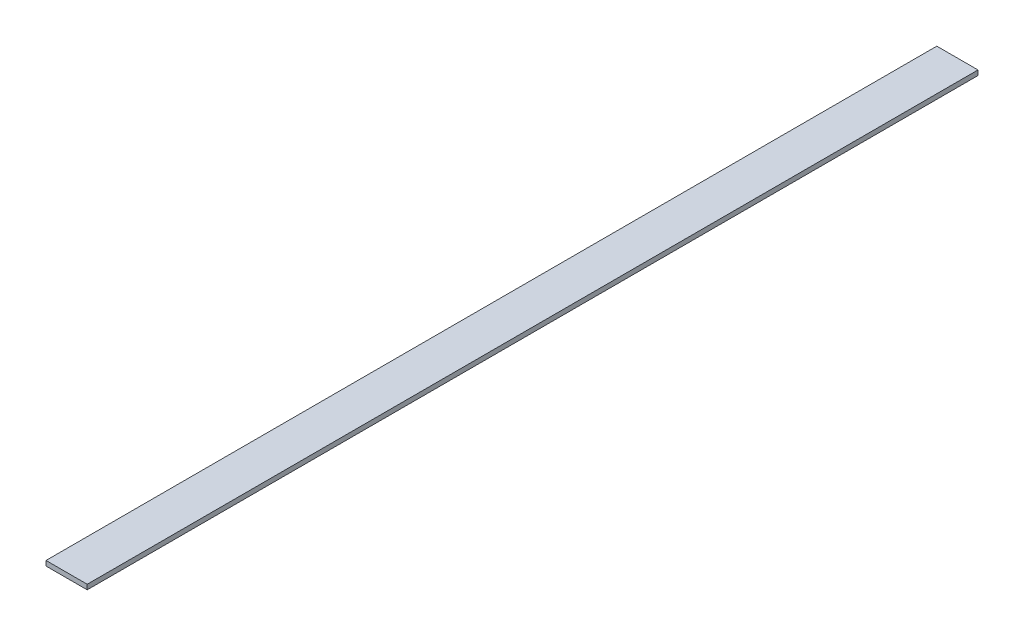
SolidWorks part; units mm, degrees
material "6063-T1"
ref_plane "Front Plane" through (0, 0, 0) normal (0, 0, 1) x (1, 0, 0)
ref_plane "Top Plane" through (0, 0, 0) normal (0, 1, 0) x (1, 0, 0)
ref_plane "Right Plane" through (0, 0, 0) normal (1, 0, 0) x (0, 0, -1)
sketch "Sketch1" plane through (0, 334.9257, 0) normal (0, 1, 0) x (1, 0, 0)
  line L0 (-25.1001, -503.8827) -> (-25.1001, 45.3173)
  line L1 (-25.1001, -169.2827) -> (-25.1001, 45.3173) construction
  line L2 (-25.1001, 45.3173) -> (0.2999, 45.3173)
  line L3 (0.2999, -529.2827) -> (0.2999, 70.7173) construction
  line L4 (0.2999, 45.3173) -> (0.2999, -503.8827)
  line L5 (-25.1001, -503.8827) -> (0.2999, -503.8827)
  point P10 (-25.1001, 36.1738)
  point P27 (0, 0)
extrude "Boss-Extrude1" add sketch "Sketch1" along normal blind 3
